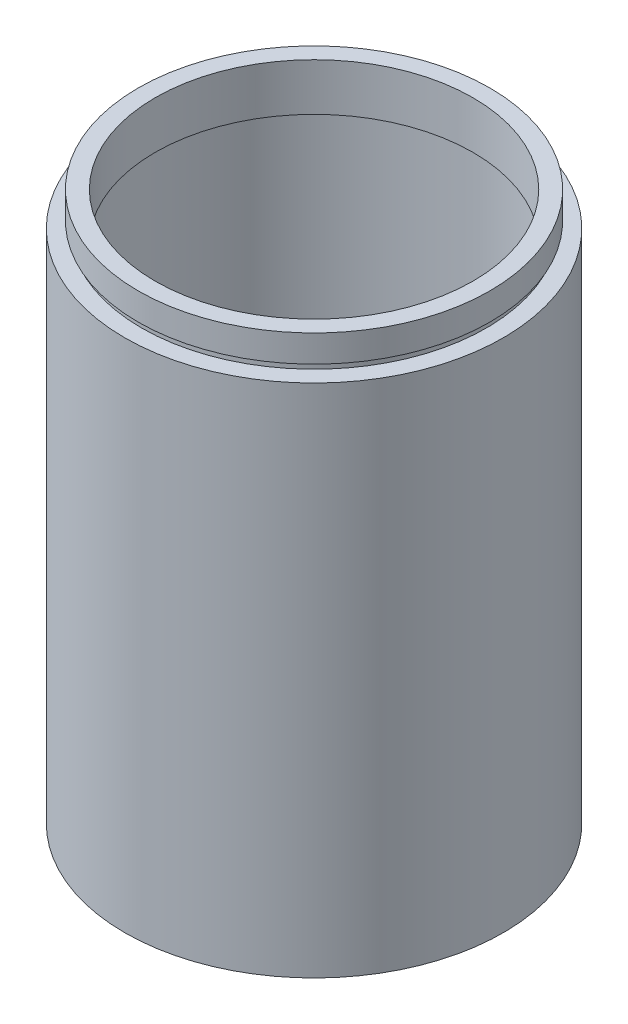
SolidWorks part; units mm, degrees
ref_plane "前视基准面" through (0, 0, 0) normal (0, 0, 1) x (1, 0, 0)
ref_plane "上视基准面" through (0, 0, 0) normal (0, 1, 0) x (1, 0, 0)
ref_plane "右视基准面" through (0, 0, 0) normal (1, 0, 0) x (0, 0, -1)
sketch "草图1" plane through (0, 0, 0) normal (0, 0, 1) x (1, 0, 0)
  line L0 (0, 161.3762) -> (0, 0) construction
  line L1 (141.7365, 0) -> (-131.7984, 0) construction
  line L2 (23.5, 81.2) -> (26, 81.2)
  line L3 (26, 81.2) -> (26, 77.2)
  line L4 (26, 77.2) -> (25.5, 77.2)
  line L5 (25.5, 77.2) -> (25.5, 76.2)
  line L6 (25.5, 76.2) -> (28, 76.2)
  line L7 (28, 76.2) -> (28, 0)
  line L8 (28, 0) -> (25.5, 0)
  line L9 (25.5, 0) -> (25.5, 73.2)
  line L10 (25.5, 73.2) -> (26.1, 73.2)
  line L11 (26.1, 73.2) -> (26.1, 74.2)
  line L12 (26.1, 74.2) -> (23.5, 74.2)
  line L13 (23.5, 74.2) -> (23.5, 81.2)
  dimension "D1" = 23.5
  dimension "D2" = 26
  dimension "D3" = 1
  dimension "D4" = 1
  dimension "D5" = 25.5
  dimension "D6" = 26.1
  dimension "D7" = 25.5
  dimension "D8" = 5
  dimension "D9" = 7
  dimension "D10" = 76.2
  dimension "D11" = 28
revolve "旋转1" add sketch "草图1" angle 360 about L0
cosmetic thread "装饰螺纹线1"
cosmetic thread "装饰螺纹线2"
cosmetic thread "装饰螺纹线3"
